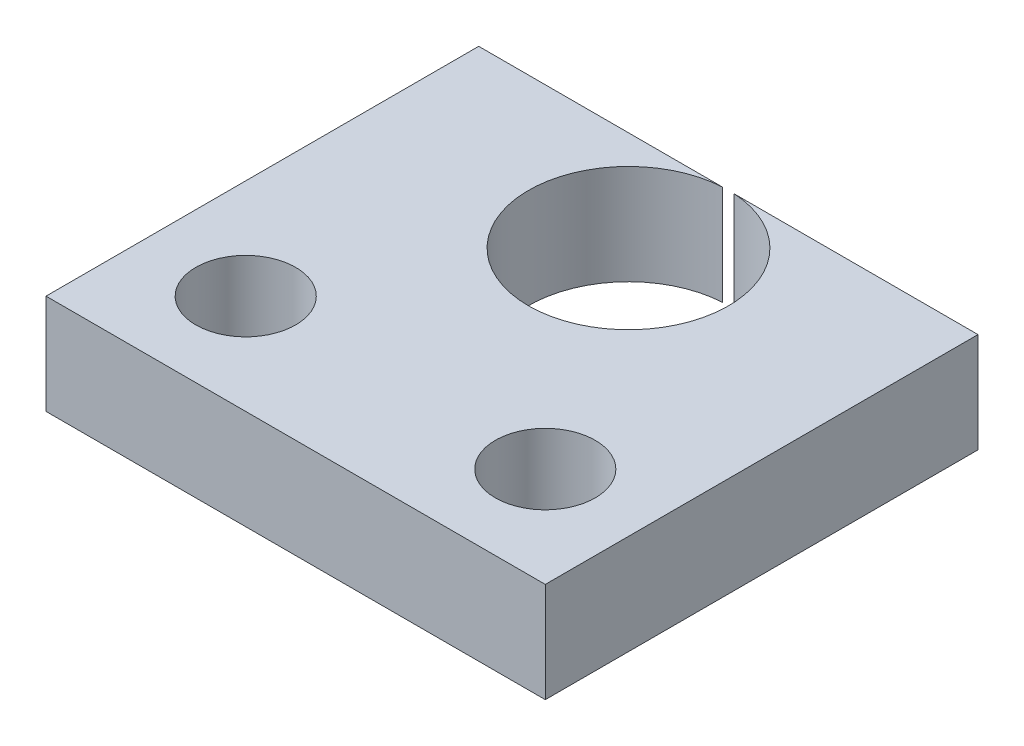
SolidWorks part; units mm, degrees
material "Balsa"
ref_plane "Plan de face" through (0, 0, 0) normal (0, 0, 1) x (1, 0, 0)
ref_plane "Plan de dessus" through (0, 0, 0) normal (0, 1, 0) x (1, 0, 0)
ref_plane "Plan de droite" through (0, 0, 0) normal (1, 0, 0) x (0, 0, -1)
sketch "Esquisse1" plane through (0, 0, 0) normal (0, 1, 0) x (1, 0, 0)
  line L1 (-7.5, 7) -> (7.5, 7)
  line L2 (-7.5, 7) -> (-7.5, -6)
  line L3 (-7.5, -6) -> (7.5, -6)
  line L4 (7.5, 7) -> (7.5, -6)
  dimension "D1" = 15
  dimension "D2" = 13
  dimension "D3" = 7.5
  dimension "D4" = 7
extrude "Boss.-Extru.1" add sketch "Esquisse1" along normal blind 3
sketch "Esquisse2" plane through (0, 3, 0) normal (0, 1, 0) x (1, 0, 0)
  line L0 (-7.5, -6) -> (7.5, -6) construction
  line L1 (-7.5, 7) -> (-7.5, -6) construction
  line L2 (7.5, -6) -> (7.5, 7) construction
  circle A0 centre (0, 4) radius 3.005
  circle A1 centre (-4.5, -3) radius 1.5
  circle A2 centre (4.5, -3) radius 1.5
  dimension "D1" = 6.01
  dimension "D2" = 4
  dimension "D3" = 3
  dimension "D4" = 3
  dimension "D5" = 3
  dimension "D6" = 3
  dimension "D7" = 3
  dimension "D8" = 3
extrude "Enlèv. mat.-Extru.1" cut sketch "Esquisse2" against normal blind 3
